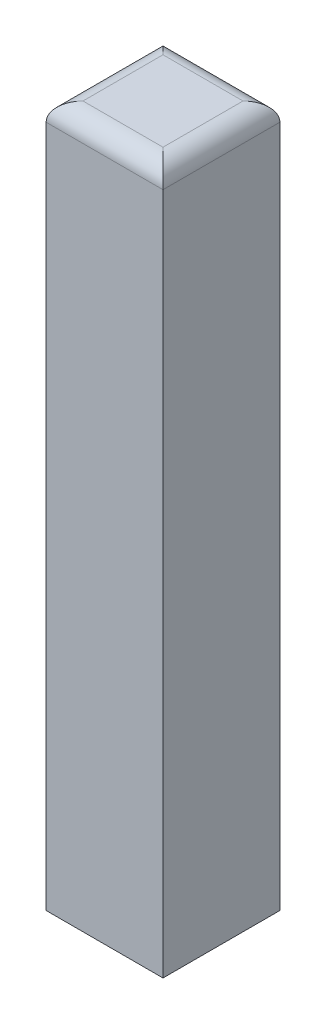
SolidWorks part; units mm, degrees
ref_plane "Front Plane" through (0, 0, 0) normal (0, 0, 1) x (1, 0, 0)
ref_plane "Top Plane" through (0, 0, 0) normal (0, 1, 0) x (1, 0, 0)
ref_plane "Right Plane" through (0, 0, 0) normal (1, 0, 0) x (0, 0, -1)
sketch "Sketch1" plane through (0, 0, 0) normal (0, 0, 1) x (1, 0, 0)
  line L0 (0, 0) -> (0, 762)
  line L1 (0, 0) -> (127, 0)
  line L2 (127, 0) -> (127, 762)
  line L3 (0, 762) -> (127, 762)
  dimension "D1" = 762
  dimension "D2" = 127
  dimension "D3" = 762
  dimension "D4" = 127
extrude "Boss-Extrude1" add sketch "Sketch1" along normal blind 127
sketch "Sketch2" plane through (0, 0, 0) normal (0, -1, 0) x (1, 0, 0)
  circle A0 centre (63.5, 63.5) radius 23.2083
  point P8 (15.171, 63.5)
fillet "Fillet3" radius 20 4 edges at (127, 762, 63.5) (63.5, 762, 127) (0, 762, 63.5) (63.5, 762, 0)
